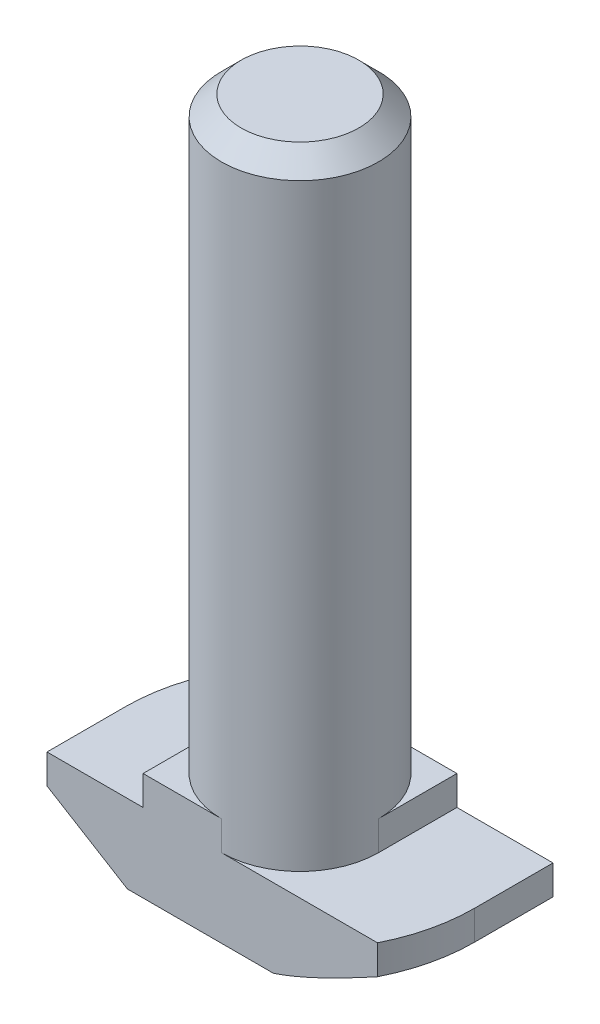
SolidWorks part; units mm, degrees
ref_plane "Спереди" through (0, 0, 0) normal (0, 0, 1) x (1, 0, 0)
ref_plane "Сверху" through (0, 0, 0) normal (0, 1, 0) x (1, 0, 0)
ref_plane "Справа" through (0, 0, 0) normal (1, 0, 0) x (0, 0, -1)
sketch "Эскиз1" plane through (0, 0, 0) normal (0, 0, 1) x (1, 0, 0)
  line L0 (8.9, 0) -> (-8.9, 0)
  line L1 (-8.9, 0) -> (-8.9, 4)
  line L2 (-8.9, 4) -> (-4, 4)
  line L3 (-4, 4) -> (-4, 5.5)
  line L4 (-4, 5.5) -> (4, 5.5)
  line L5 (0, 5.5) -> (0, 0) construction
  line L6 (4, 4) -> (4, 5.5)
  line L7 (8.9, 4) -> (4, 4)
  line L8 (8.9, 0) -> (8.9, 4)
  point P12 (-8.25, 2.6435)
  point P13 (-4, 3.6993)
  dimension "D1" = 8
  dimension "D2" = 17.8
  dimension "D3" = 5.5
  dimension "D4" = 1.5
extrude "Бобышка-Вытянуть1" add sketch "Эскиз1" along normal mid plane 8
sketch "Эскиз3" plane through (0, 5.5, 0) normal (0, 1, 0) x (1, 0, 0)
  line L1 (4, 4) -> (-4, 4) construction
  line L2 (-4, 0) -> (-4, 4)
  line L3 (-4, 4) -> (0, 4)
  line L4 (0, -4) -> (4, -4)
  line L5 (4, -4) -> (-4, -4) construction
  line L6 (4, -4) -> (4, 0)
  line L7 (4, -4) -> (4, 4) construction
  arc A0 (-4, 0) -> (0, 4) centre (0, 0) cw
  arc A1 (4, 0) -> (0, -4) centre (0, 0) cw
extrude "Вырез-Вытянуть1" cut sketch "Эскиз3" against normal up to surface (1.5 mm away) up to face at (-6.45, 4, 0)
sketch "Эскиз2" plane through (0, 5.5, 0) normal (0, 1, 0) x (1, 0, 0)
  circle A0 centre (0, 0) radius 4
  dimension "D1" = 8
extrude "Бобышка-Вытянуть2" add sketch "Эскиз2" along normal blind 30
cosmetic thread "Условное изображение резьбы1" parameters "D1"=30, "D2"=6.619
sketch "Эскиз4" plane through (0, 4, 0) normal (0, 1, 0) x (1, 0, 0)
  line L0 (-8.9, -4) -> (-8.9, 4) construction
  line L1 (8.9, -4) -> (8.9, 4) construction
  line L2 (-7.9505, 4) -> (-8.9, 4)
  line L3 (-8.9, 4) -> (-8.9, 0)
  line L4 (7.9505, -4) -> (8.9, -4)
  line L5 (8.9, -4) -> (8.9, 0)
  arc A0 (-8.9, 0) -> (-7.9505, 4) centre (0, 0) cw
  arc A1 (8.9, 0) -> (7.9505, -4) centre (0, 0) cw
extrude "Вырез-Вытянуть2" cut sketch "Эскиз4" against normal through all
sketch "Эскиз5" plane through (0, 0, 4) normal (0, 0, 1) x (1, 0, 0)
  line L0 (-8.9, 2.5) -> (-4.8, 0)
  line L1 (-8.9, 4) -> (-8.9, 0) construction
  line L2 (-8.9, 0) -> (7.9505, 0) construction
  line L3 (-4.8, 0) -> (-8.9, 0)
  line L4 (-8.9, 0) -> (-8.9, 2.5)
  line L6 (-4, 4) -> (-8.9, 4) construction
  line L7 (-4, 5.5) -> (-4, 4) construction
  point P6 (-4.9519, 0)
  point P9 (0, 0)
  point P10 (-4.6154, 0)
  point P12 (-8.25, 2.2665)
  point P15 (0, 0)
  dimension "D1" = 1.5
  dimension "D2" = 0.8
sketch "Эскиз6" plane through (0, 0, 0) normal (0, -1, 0) x (1, 0, 0)
  line L0 (0, -8.9) -> (8.9, -8.9)
  line L1 (8.9, -8.9) -> (8.9, 0)
  line L2 (0, 8.9) -> (-8.9, 8.9)
  line L3 (-8.9, 8.9) -> (-8.9, 0)
  arc A0 (-8.9, 0) -> (0, -8.9) centre (0, 0) ccw
  arc A1 (8.9, 0) -> (0, 8.9) centre (0, 0) ccw
  point P10 (0, 0)
sweep "Вырез-По траектории1" cut profiles "Эскиз5" path "Эскиз6"
chamfer "Фаска2" distance 1 angle 45 1 edges at (0, 35.5, 4)
